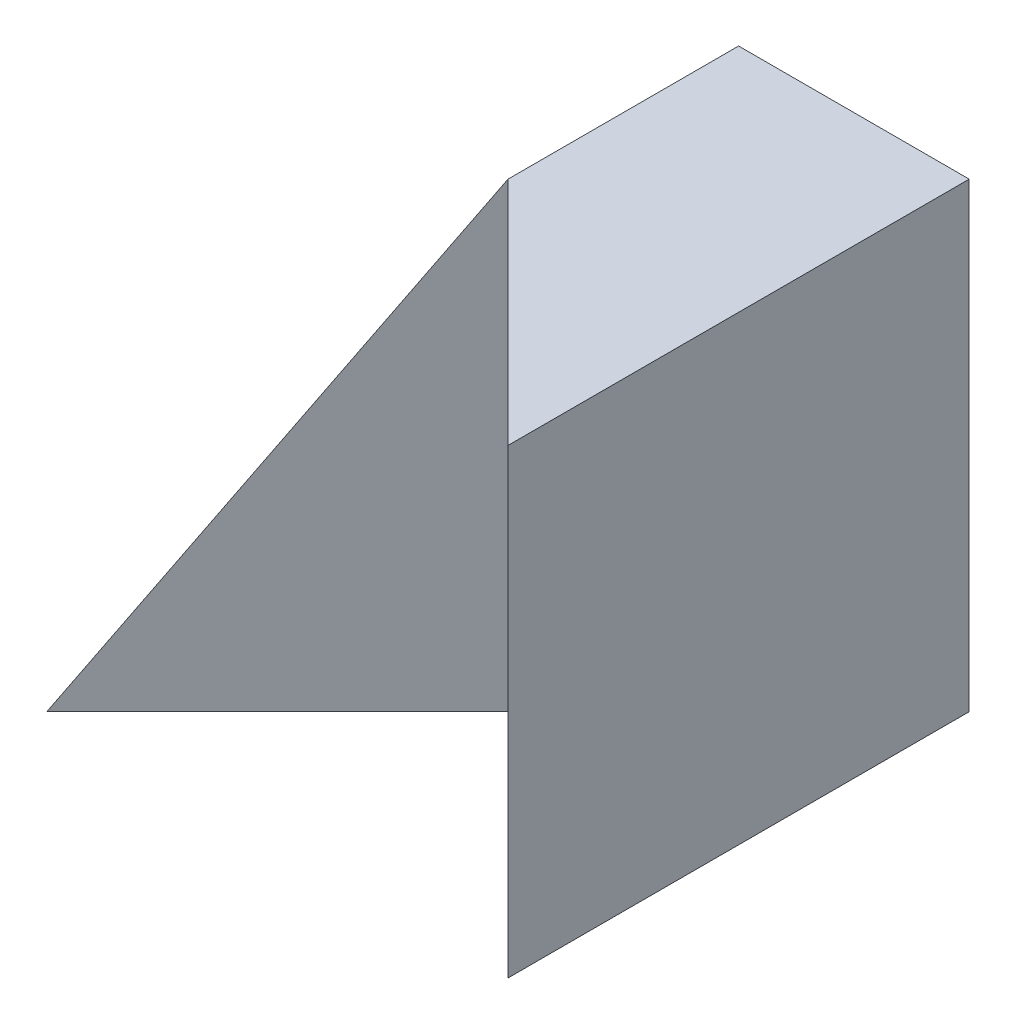
SolidWorks part; units mm, degrees
ref_plane "Front Plane" through (0, 0, 0) normal (0, 0, 1) x (1, 0, 0)
ref_plane "Top Plane" through (0, 0, 0) normal (0, 1, 0) x (1, 0, 0)
ref_plane "Right Plane" through (0, 0, 0) normal (1, 0, 0) x (0, 0, -1)
sketch "Sketch1" plane through (0, 0, 0) normal (0, 0, 1) x (1, 0, 0)
  line L1 (0, 0) -> (40, 0)
  line L2 (0, 0) -> (0, 40)
  line L3 (0, 40) -> (40, 40)
  line L4 (40, 0) -> (40, 40)
  dimension "D1" = 40
  dimension "D2" = 40
extrude "Boss-Extrude1" add sketch "Sketch1" along normal blind 40
sketch "Sketch2" plane through (0, 0, 40) normal (0, 0, 1) x (1, 0, 0)
  line L0 (0, 0) -> (20, 40)
  line L1 (40, 40) -> (0, 40) construction
  line L2 (20, 40) -> (0, 40)
  line L3 (0, 40) -> (0, 0)
extrude "Cut-Extrude1" cut sketch "Sketch2" against normal blind 40
sketch "Sketch3" plane through (0, 0, 0) normal (0, -1, 0) x (1, 0, 0)
  line L0 (0, 40) -> (20, 20)
  line L1 (20, 20) -> (40, 40)
  line L2 (40, 40) -> (0, 40)
  dimension "D1" = 20
  dimension "D2" = 20
extrude "Cut-Extrude2" cut sketch "Sketch3" against normal blind 40
